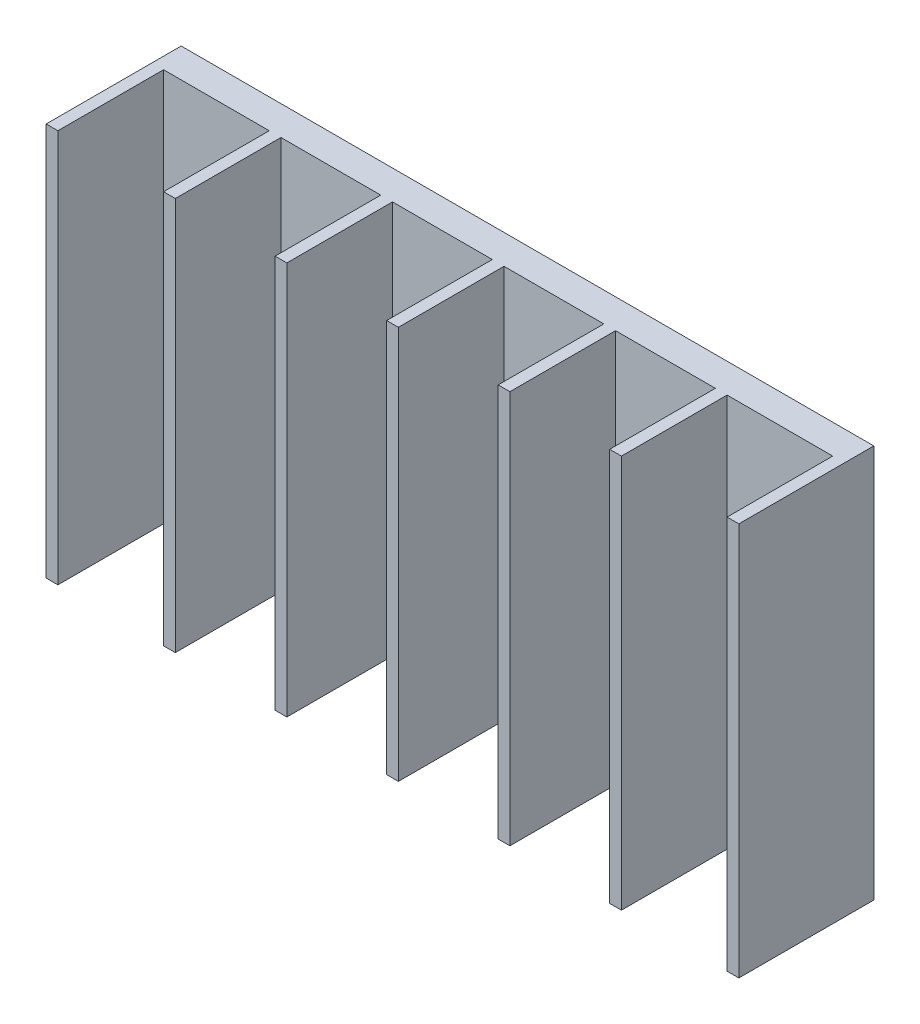
SolidWorks part; units mm, degrees
ref_plane "Front Plane" through (0, 0, 0) normal (0, 0, 1) x (1, 0, 0)
ref_plane "Top Plane" through (0, 0, 0) normal (0, 1, 0) x (1, 0, 0)
ref_plane "Right Plane" through (0, 0, 0) normal (1, 0, 0) x (0, 0, -1)
sketch "Sketch1" plane through (0, 0, 0) normal (0, 0, 1) x (1, 0, 0)
  line L1 (-57, 33.5) -> (57, 33.5)
  line L2 (-57, 33.5) -> (-57, -33.5)
  line L3 (-57, -33.5) -> (57, -33.5)
  line L4 (57, 33.5) -> (57, -33.5)
  line L5 (-57, 33.5) -> (57, -33.5) construction
  line L6 (-57, -33.5) -> (57, 33.5) construction
  point P0 (0, 0)
  dimension "D1" = 67
  dimension "D2" = 114
extrude "Boss-Extrude1" add sketch "Sketch1" along normal mid plane 5
sketch "Sketch2" plane through (0, 0, 2.5) normal (0, 0, 1) x (1, 0, 0)
  line L0 (-57, -33.5) -> (57, -33.5) construction
  line L1 (-37, 33.5) -> (-39, 33.5)
  line L2 (-37, 33.5) -> (-37, -33.5)
  line L3 (-37, -33.5) -> (-39, -33.5)
  line L4 (-39, 33.5) -> (-39, -33.5)
  line L5 (-37, 33.5) -> (-39, -33.5) construction
  line L6 (-37, -33.5) -> (-39, 33.5) construction
  line L7 (-57, 33.5) -> (-57, -33.5) construction
  point P0 (-38, 0)
  dimension "D1" = 2
  dimension "D2" = 67
  dimension "D3" = 18
extrude "Boss-Extrude2" add sketch "Sketch2" along normal blind 18
pattern_linear "LPattern1" count 5 spacing 19 along (1, 0, 0) of "Boss-Extrude2"
sketch "Sketch3" plane through (-57, 0, 0) normal (-1, 0, 0) x (0, 0, 1)
  line L1 (-2.5, 33.5) -> (20.5, 33.5)
  line L2 (-2.5, 33.5) -> (-2.5, -33.5)
  line L3 (-2.5, -33.5) -> (20.5, -33.5)
  line L4 (20.5, 33.5) -> (20.5, -33.5)
  line L5 (-2.5, 33.5) -> (20.5, -33.5) construction
  line L6 (-2.5, -33.5) -> (20.5, 33.5) construction
  point P4 (9, 0)
extrude "Boss-Extrude3" add sketch "Sketch3" along normal blind 2
mirror "Mirror1" about plane through (0, 0, 0) normal (1, 0, 0) of "Boss-Extrude3"
